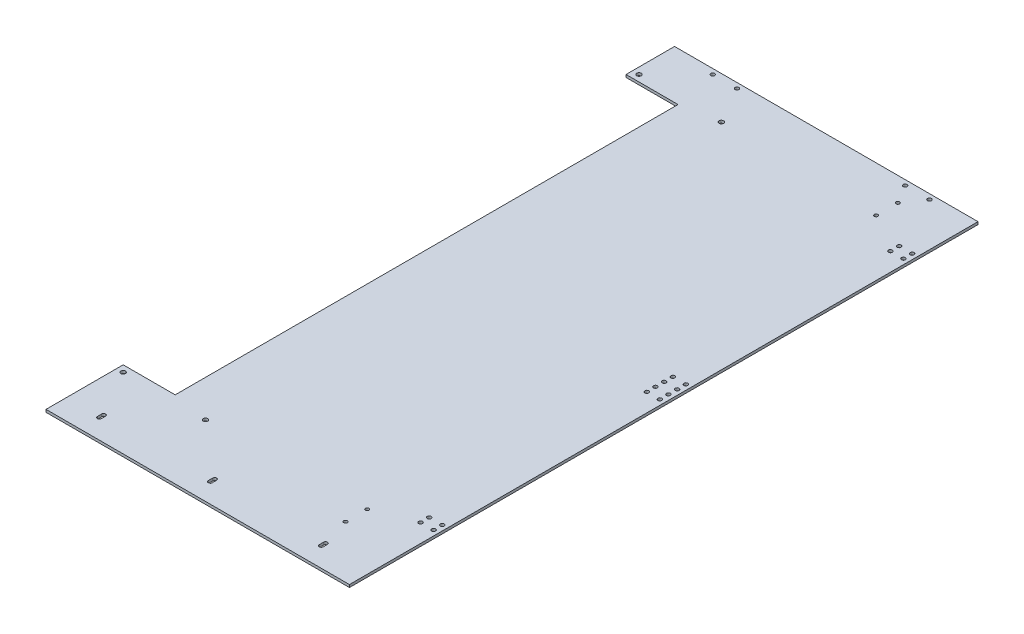
SolidWorks part; units mm, degrees
material "6061 合金"
ref_plane "前视基准面" through (0, 0, 0) normal (0, 0, 1) x (1, 0, 0)
ref_plane "上视基准面" through (0, 0, 0) normal (0, 1, 0) x (1, 0, 0)
ref_plane "右视基准面" through (0, 0, 0) normal (1, 0, 0) x (0, 0, -1)
sketch "草图1" plane through (0, 0, 0) normal (0, 0, 1) x (1, 0, 0)
  line L1 (-18.5263, 6.2355) -> (331.4737, 6.2355)
  line L2 (-18.5263, 6.2355) -> (-18.5263, 3.2355)
  line L3 (-18.5263, 3.2355) -> (331.4737, 3.2355)
  line L4 (331.4737, 6.2355) -> (331.4737, 3.2355)
  dimension "D1" = 3
  dimension "D2" = 350
extrude "凸台-拉伸1" add sketch "草图1" along normal blind 725
sketch "草图2" plane through (0, 6.2355, 0) normal (0, 1, 0) x (1, 0, 0)
  line L0 (331.4737, -725) -> (-18.5263, -725) construction
  line L1 (411.2526, -48.5) -> (-140.5458, -48.5) construction
  line L2 (411.2526, -643.5) -> (-140.5458, -643.5) construction
  line L3 (331.4737, 0) -> (-18.5263, 0) construction
  line L4 (-127.7206, -700) -> (411.2526, -700) construction
  line L5 (-18.5263, -725) -> (-18.5263, 0) construction
  line L6 (28.2774, -702.5) -> (14.9002, -702.5) construction
  line L7 (-18.5263, -56) -> (41.4737, -56)
  line L8 (-18.5263, -56) -> (-18.5263, -636)
  line L9 (-18.5263, -636) -> (41.4737, -636)
  line L10 (41.4737, -56) -> (41.4737, -636)
  line L11 (372.497, -336) -> (290.5463, -336) construction
  line L13 (331.4737, -725) -> (331.4737, 0) construction
  line L14 (367.4379, -75) -> (282.235, -75) construction
  line L15 (377.0462, -205.5) -> (282.235, -205.5) construction
  line L16 (344.9341, -6) -> (-30.3419, -6) construction
  line L17 (156.4737, -114.4028) -> (156.4737, 89.021) construction
  line L18 (479.1294, -346) -> (211.3096, -346) construction
  line L19 (18.2237, -702.5) -> (18.2237, -697.5)
  line L21 (22.7237, -702.5) -> (22.7237, -697.5)
  line L22 (20.4737, -691.2584) -> (20.4737, -707.7123) construction
  line L23 (150.7237, -702.5) -> (150.7237, -697.5)
  line L24 (148.4737, -691.2584) -> (148.4737, -707.7123) construction
  line L25 (146.2237, -702.5) -> (146.2237, -697.5)
  line L26 (156.2774, -702.5) -> (142.9002, -702.5) construction
  line L27 (284.2774, -702.5) -> (270.9002, -702.5) construction
  line L28 (278.7237, -702.5) -> (278.7237, -697.5)
  line L29 (276.4737, -691.2584) -> (276.4737, -707.7123) construction
  line L30 (274.2237, -702.5) -> (274.2237, -697.5)
  line L31 (331.4737, -725) -> (331.4737, 0) construction
  line L32 (303.1009, -52.5) -> (324.5716, -52.5) construction
  line L33 (302.1096, -639.5) -> (328.0307, -639.5) construction
  circle A0 centre (-11.0263, -48.5) radius 2.6
  circle A1 centre (83.9737, -48.5) radius 2.6
  circle A2 centre (-11.0263, -643.5) radius 2.6
  circle A3 centre (83.9737, -643.5) radius 2.6
  circle A13 centre (325.4737, -341) radius 2.25
  circle A14 centre (310.4737, -341) radius 2.25
  circle A15 centre (310.4737, -331) radius 2.25
  circle A16 centre (325.4737, -331) radius 2.25
  circle A17 centre (310.4737, -80) radius 2.25
  circle A18 centre (310.4737, -70) radius 2.25
  circle A19 centre (325.4737, -70) radius 2.25
  circle A20 centre (325.4737, -80) radius 2.25
  circle A21 centre (281.4737, -6) radius 2.25
  circle A22 centre (253.4737, -6) radius 2.25
  circle A23 centre (31.4737, -6) radius 2.25
  circle A24 centre (59.4737, -6) radius 2.25
  circle A25 centre (325.4737, -351) radius 2.25
  circle A26 centre (310.4737, -351) radius 2.25
  circle A27 centre (325.4737, -361) radius 2.25
  circle A28 centre (310.4737, -361) radius 2.25
  circle A29 centre (310.4737, -612) radius 2.25
  circle A30 centre (325.4737, -612) radius 2.25
  circle A31 centre (325.4737, -622) radius 2.25
  circle A32 centre (310.4737, -622) radius 2.25
  arc A33 (18.2237, -702.5) -> (22.7237, -702.5) centre (20.4737, -702.5) ccw
  arc A34 (22.7237, -697.5) -> (18.2237, -697.5) centre (20.4737, -697.5) ccw
  arc A35 (146.2237, -702.5) -> (150.7237, -702.5) centre (148.4737, -702.5) ccw
  arc A36 (150.7237, -697.5) -> (146.2237, -697.5) centre (148.4737, -697.5) ccw
  arc A37 (274.2237, -702.5) -> (278.7237, -702.5) centre (276.4737, -702.5) ccw
  arc A38 (278.7237, -697.5) -> (274.2237, -697.5) centre (276.4737, -697.5) ccw
  circle A39 centre (266.4737, -639.5) radius 2.05
  circle A40 centre (266.4737, -664.5) radius 2.05
  circle A41 centre (266.4737, -52.5) radius 2.05
  circle A42 centre (266.4737, -27.5) radius 2.05
  dimension "D3" = 5.2
  dimension "D4" = 95
  dimension "D5" = 7.5
  dimension "D6" = 95
  dimension "D7" = 7.5
  dimension "D8" = 5.2
  dimension "D14" = 4.5
  dimension "D15" = 5
  dimension "D16" = 4.5
  dimension "D17" = 4.5
  dimension "D18" = 5
  dimension "D21" = 5
  dimension "D22" = 4.5
  dimension "D26" = 28
  dimension "D27" = 50
  dimension "D28" = 4.5
  dimension "D32" = 4.1
  dimension "D33" = 25
  dimension "D34" = 65
  dimension "D35" = 4.1
  dimension "D36" = 25
  dimension "D37" = 65
  dimension "D38" = 587
  dimension "D1" = 48.5
  dimension "D2" = 81.5
  dimension "D9" = 7.5
  dimension "D10" = 7.5
  dimension "D11" = 60
  dimension "D12" = 10
  dimension "D13" = 25
  dimension "D19" = 15
  dimension "D20" = 6
  dimension "D23" = 128
  dimension "D24" = 261
  dimension "D25" = 6
  dimension "D29" = 5
  dimension "D30" = 128
  dimension "D31" = 55
extrude "切除-拉伸1" cut sketch "草图2" against normal blind 10
